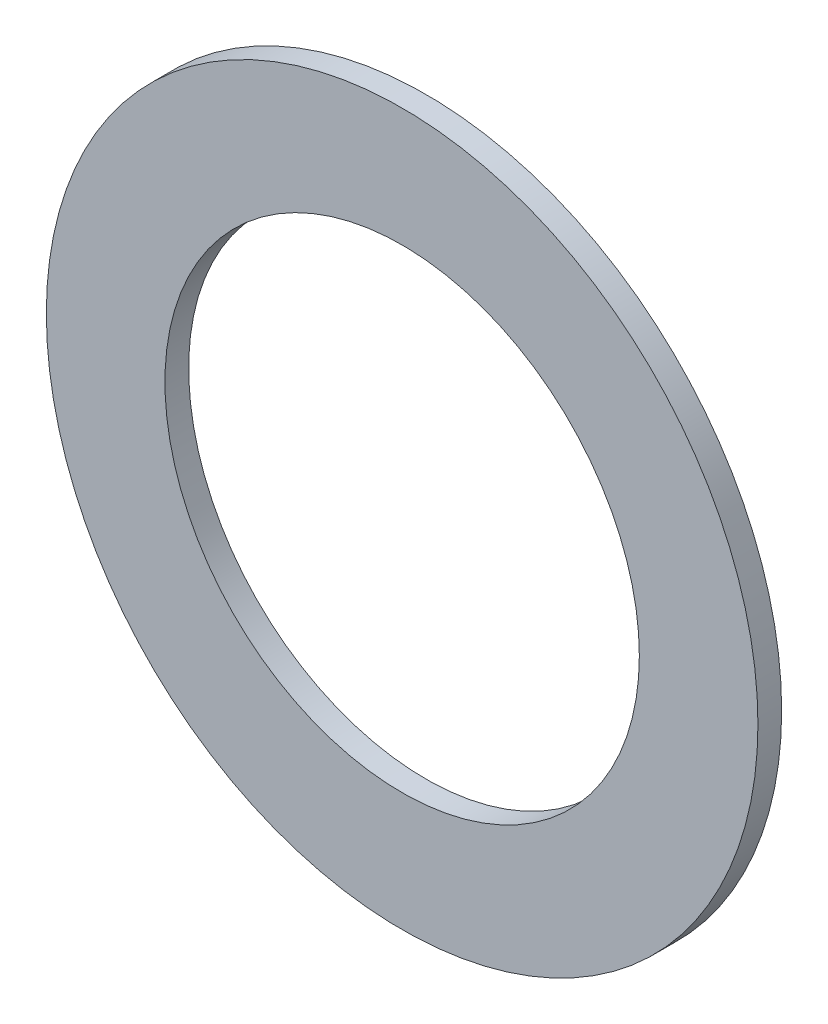
SolidWorks part; units mm, degrees
material "AISI 304"
ref_plane "前视基准面" through (0, 0, 0) normal (0, 0, 1) x (1, 0, 0)
ref_plane "上视基准面" through (0, 0, 0) normal (0, 1, 0) x (1, 0, 0)
ref_plane "右视基准面" through (0, 0, 0) normal (1, 0, 0) x (0, 0, -1)
sketch "草图1" plane through (0, 0, 0) normal (0, 0, 1) x (1, 0, 0)
  circle A0 centre (0, 0) radius 3
  circle A1 centre (0, 0) radius 2
  dimension "D1" = 4
  dimension "D2" = 6
extrude "凸台-拉伸1" add sketch "草图1" along normal blind 0.2
move or copy body "实体-移动/复制1" [suppressed] bodies to move or copy 106
